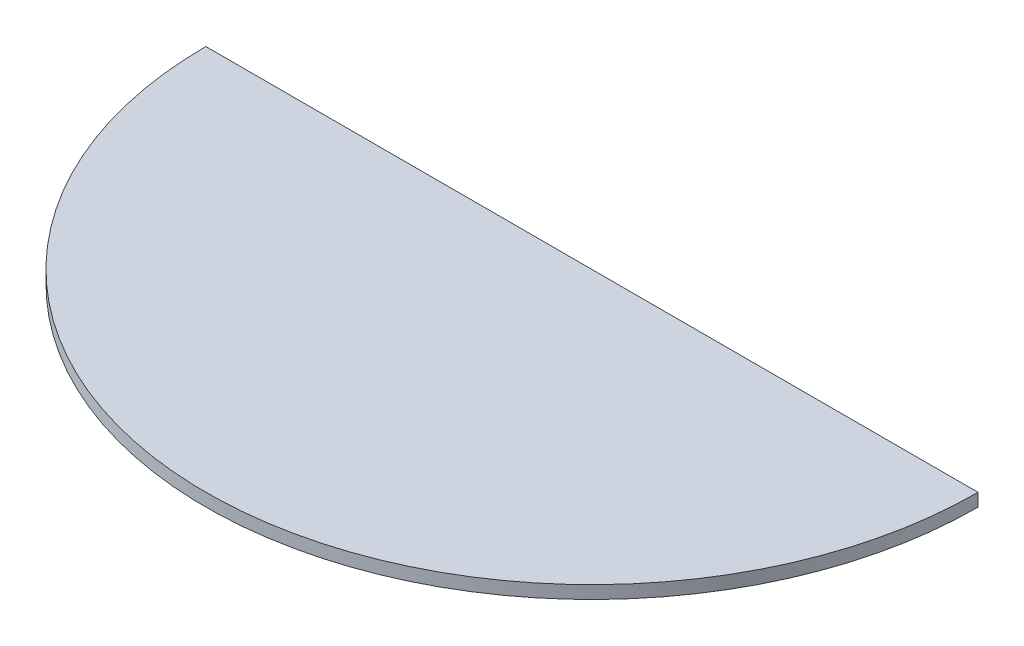
SolidWorks part; units mm, degrees
ref_plane "Face" through (0, 0, 0) normal (0, 0, 1) x (1, 0, 0)
ref_plane "Dessus" through (0, 0, 0) normal (0, 1, 0) x (1, 0, 0)
ref_plane "Droite" through (0, 0, 0) normal (1, 0, 0) x (0, 0, -1)
sketch "Esquisse1" plane through (0, 0, 0) normal (0, 1, 0) x (1, 0, 0)
  line L0 (0, 0) -> (600, 0)
  arc A0 (0, 0) -> (600, 0) centre (300, 0) ccw
  dimension "D1" = 600
extrude "Extrusion1" add sketch "Esquisse1" along normal blind 10 contours L0 A0
